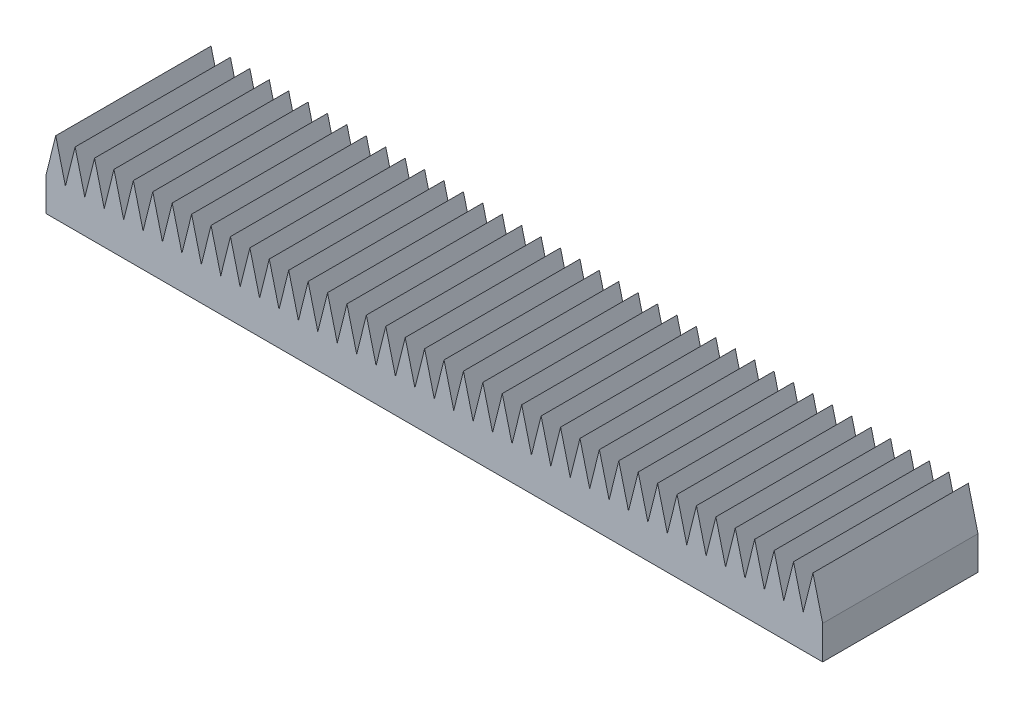
SolidWorks part; units mm, degrees
ref_plane "Front Plane" through (0, 0, 0) normal (0, 0, 1) x (1, 0, 0)
ref_plane "Top Plane" through (0, 0, 0) normal (0, 1, 0) x (1, 0, 0)
ref_plane "Right Plane" through (0, 0, 0) normal (1, 0, 0) x (0, 0, -1)
sketch "Sketch1" plane through (0, 0, 0) normal (0, 0, 1) x (1, 0, 0)
  line L0 (-100, 4.3083) -> (-97.5, 14.3083)
  line L2 (-100, 4.3083) -> (-100, -4.3083)
  line L3 (-100, -4.3083) -> (100, -4.3083)
  line L4 (100, 4.3083) -> (100, -4.3083)
  line L7 (-97.5, 14.3083) -> (-95, 4.3083)
  line L8 (-92.5, 14.3083) -> (-90, 4.3083)
  line L9 (-95, 4.3083) -> (-92.5, 14.3083)
  line L10 (-87.5, 14.3083) -> (-85, 4.3083)
  line L11 (-90, 4.3083) -> (-87.5, 14.3083)
  line L12 (-82.5, 14.3083) -> (-80, 4.3083)
  line L13 (-85, 4.3083) -> (-82.5, 14.3083)
  line L14 (-77.5, 14.3083) -> (-75, 4.3083)
  line L15 (-80, 4.3083) -> (-77.5, 14.3083)
  line L16 (-72.5, 14.3083) -> (-70, 4.3083)
  line L17 (-75, 4.3083) -> (-72.5, 14.3083)
  line L18 (-67.5, 14.3083) -> (-65, 4.3083)
  line L19 (-70, 4.3083) -> (-67.5, 14.3083)
  line L20 (-62.5, 14.3083) -> (-60, 4.3083)
  line L21 (-65, 4.3083) -> (-62.5, 14.3083)
  line L22 (-57.5, 14.3083) -> (-55, 4.3083)
  line L23 (-60, 4.3083) -> (-57.5, 14.3083)
  line L24 (-52.5, 14.3083) -> (-50, 4.3083)
  line L25 (-55, 4.3083) -> (-52.5, 14.3083)
  line L26 (-47.5, 14.3083) -> (-45, 4.3083)
  line L27 (-50, 4.3083) -> (-47.5, 14.3083)
  line L28 (-42.5, 14.3083) -> (-40, 4.3083)
  line L29 (-45, 4.3083) -> (-42.5, 14.3083)
  line L30 (-37.5, 14.3083) -> (-35, 4.3083)
  line L31 (-40, 4.3083) -> (-37.5, 14.3083)
  line L32 (-32.5, 14.3083) -> (-30, 4.3083)
  line L33 (-35, 4.3083) -> (-32.5, 14.3083)
  line L34 (-27.5, 14.3083) -> (-25, 4.3083)
  line L35 (-30, 4.3083) -> (-27.5, 14.3083)
  line L36 (-22.5, 14.3083) -> (-20, 4.3083)
  line L37 (-25, 4.3083) -> (-22.5, 14.3083)
  line L38 (-17.5, 14.3083) -> (-15, 4.3083)
  line L39 (-20, 4.3083) -> (-17.5, 14.3083)
  line L40 (-12.5, 14.3083) -> (-10, 4.3083)
  line L41 (-15, 4.3083) -> (-12.5, 14.3083)
  line L42 (-7.5, 14.3083) -> (-5, 4.3083)
  line L43 (-10, 4.3083) -> (-7.5, 14.3083)
  line L44 (-2.5, 14.3083) -> (0, 4.3083)
  line L45 (-5, 4.3083) -> (-2.5, 14.3083)
  line L46 (2.5, 14.3083) -> (5, 4.3083)
  line L47 (0, 4.3083) -> (2.5, 14.3083)
  line L48 (7.5, 14.3083) -> (10, 4.3083)
  line L49 (5, 4.3083) -> (7.5, 14.3083)
  line L50 (12.5, 14.3083) -> (15, 4.3083)
  line L51 (10, 4.3083) -> (12.5, 14.3083)
  line L52 (17.5, 14.3083) -> (20, 4.3083)
  line L53 (15, 4.3083) -> (17.5, 14.3083)
  line L54 (22.5, 14.3083) -> (25, 4.3083)
  line L55 (20, 4.3083) -> (22.5, 14.3083)
  line L56 (27.5, 14.3083) -> (30, 4.3083)
  line L57 (25, 4.3083) -> (27.5, 14.3083)
  line L58 (32.5, 14.3083) -> (35, 4.3083)
  line L59 (30, 4.3083) -> (32.5, 14.3083)
  line L60 (37.5, 14.3083) -> (40, 4.3083)
  line L61 (35, 4.3083) -> (37.5, 14.3083)
  line L62 (42.5, 14.3083) -> (45, 4.3083)
  line L63 (40, 4.3083) -> (42.5, 14.3083)
  line L64 (47.5, 14.3083) -> (50, 4.3083)
  line L65 (45, 4.3083) -> (47.5, 14.3083)
  line L66 (52.5, 14.3083) -> (55, 4.3083)
  line L67 (50, 4.3083) -> (52.5, 14.3083)
  line L68 (57.5, 14.3083) -> (60, 4.3083)
  line L69 (55, 4.3083) -> (57.5, 14.3083)
  line L70 (62.5, 14.3083) -> (65, 4.3083)
  line L71 (60, 4.3083) -> (62.5, 14.3083)
  line L72 (67.5, 14.3083) -> (70, 4.3083)
  line L73 (65, 4.3083) -> (67.5, 14.3083)
  line L74 (72.5, 14.3083) -> (75, 4.3083)
  line L75 (70, 4.3083) -> (72.5, 14.3083)
  line L76 (77.5, 14.3083) -> (80, 4.3083)
  line L77 (75, 4.3083) -> (77.5, 14.3083)
  line L78 (82.5, 14.3083) -> (85, 4.3083)
  line L79 (80, 4.3083) -> (82.5, 14.3083)
  line L80 (87.5, 14.3083) -> (90, 4.3083)
  line L81 (85, 4.3083) -> (87.5, 14.3083)
  line L82 (92.5, 14.3083) -> (95, 4.3083)
  line L83 (90, 4.3083) -> (92.5, 14.3083)
  line L84 (97.5, 14.3083) -> (100, 4.3083)
  line L85 (95, 4.3083) -> (97.5, 14.3083)
  point P0 (0, 0)
  point P6 (0, 0)
  dimension "D1" = 5
  dimension "D3" = 40
extrude "Boss-Extrude1" add sketch "Sketch1" along normal blind 40
